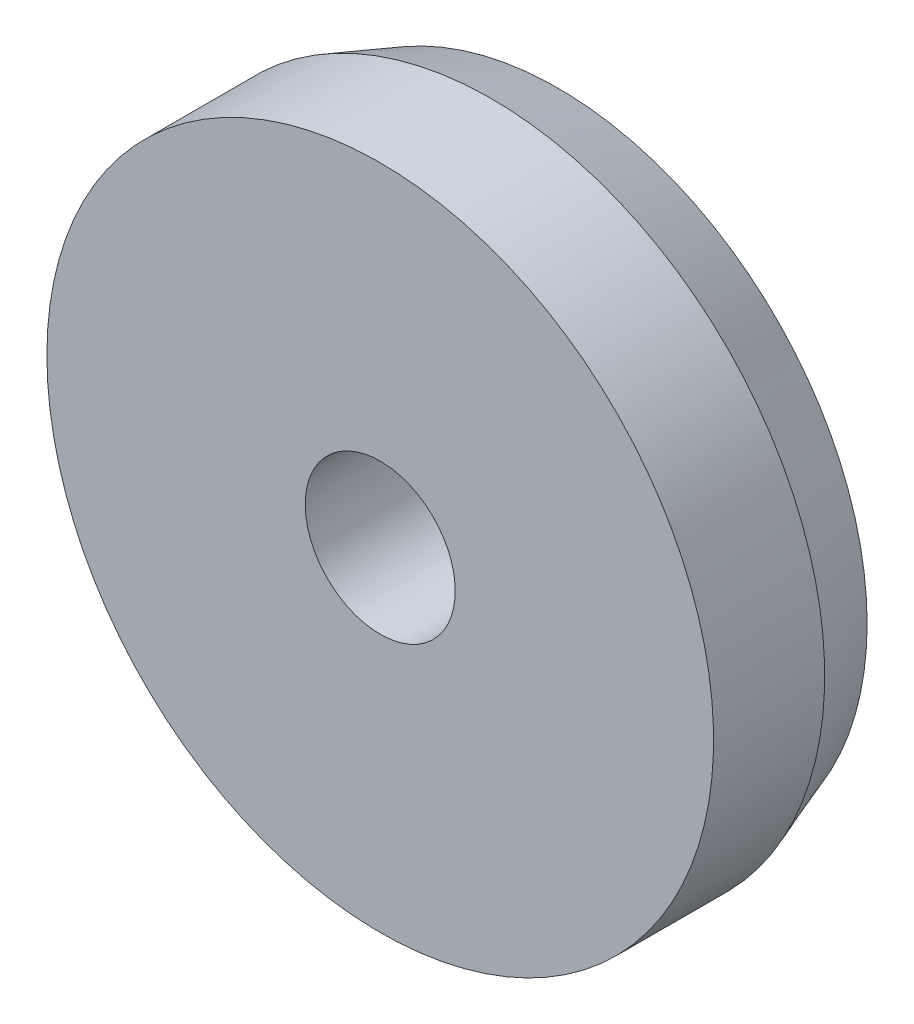
SolidWorks part; units mm, degrees
ref_plane "Alzado" through (0, 0, 0) normal (0, 0, 1) x (1, 0, 0)
ref_plane "Planta" through (0, 0, 0) normal (0, 1, 0) x (1, 0, 0)
ref_plane "Vista lateral" through (0, 0, 0) normal (1, 0, 0) x (0, 0, -1)
ref_plane "Plane1" through (0, -6.0741, 0) normal (0, -1, 0) x (1, 0, 0)
sketch "Sketch1" plane through (0, -6.0741, 0) normal (0, -1, 0) x (1, 0, 0)
  line L0 (-2.0623, -1.87) -> (-2.0623, -1.67)
  line L1 (-2.0623, -1.67) -> (-2.5273, -1.67)
  line L2 (-2.5273, -1.67) -> (-2.5273, -1.87)
  line L3 (-2.2123, -1.99) -> (-2.1059, -1.99)
  line L4 (-2.1059, -1.99) -> (-2.0623, -1.87)
  line L5 (-2.6623, -1.67) -> (-2.6623, -1.99) construction
  arc A0 (-2.5273, -1.87) -> (-2.2123, -1.99) centre (-2.6623, -2.6978) cw
  dimension "D1" = 0.8387
  dimension "D2" = 0.135
  dimension "D3" = 0.45
  dimension "D4" = 0.5563
  dimension "D5" = 0.6
  dimension "D6" = 0.2
revolve "Revolve1" add sketch "Sketch1" angle 360 about L5
